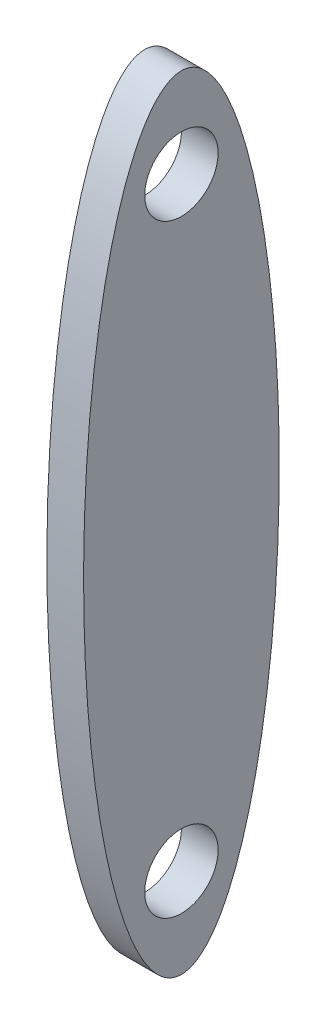
SolidWorks part; units mm, degrees
ref_plane "Front Plane" through (0, 0, 0) normal (0, 0, 1) x (1, 0, 0)
ref_plane "Top Plane" through (0, 0, 0) normal (0, 1, 0) x (1, 0, 0)
ref_plane "Right Plane" through (0, 0, 0) normal (1, 0, 0) x (0, 0, -1)
sketch "Sketch2" plane through (0, 0, 0) normal (1, 0, 0) x (0, 0, -1)
  ellipse E0 centre (0, 0) end of major axis (0, 50.8) minor radius 12.7
  point P1 (0, 0)
  point P7 (0, 0)
extrude "Boss-Extrude1" add sketch "Sketch2" along normal blind 4.7625
sketch "Sketch3" plane through (4.7625, 0, 0) normal (1, 0, 0) x (0, 0, -1)
  circle A0 centre (0, 39.1764) radius 4.7625
  ellipse E0 centre (0, 0) end of major axis (0, 50.8) minor radius 12.7 construction
  point P2 (0, 0)
  point P9 (0, 0)
extrude "Cut-Extrude1" cut sketch "Sketch3" against normal through all contours A0
sketch "Sketch4" plane through (0, 0, 0) normal (1, 0, 0) x (0, 0, -1)
  circle A0 centre (0, -39.1764) radius 4.7625
  point P2 (0, 0)
extrude "Cut-Extrude10" cut sketch "Sketch4" along normal through all contours A0
